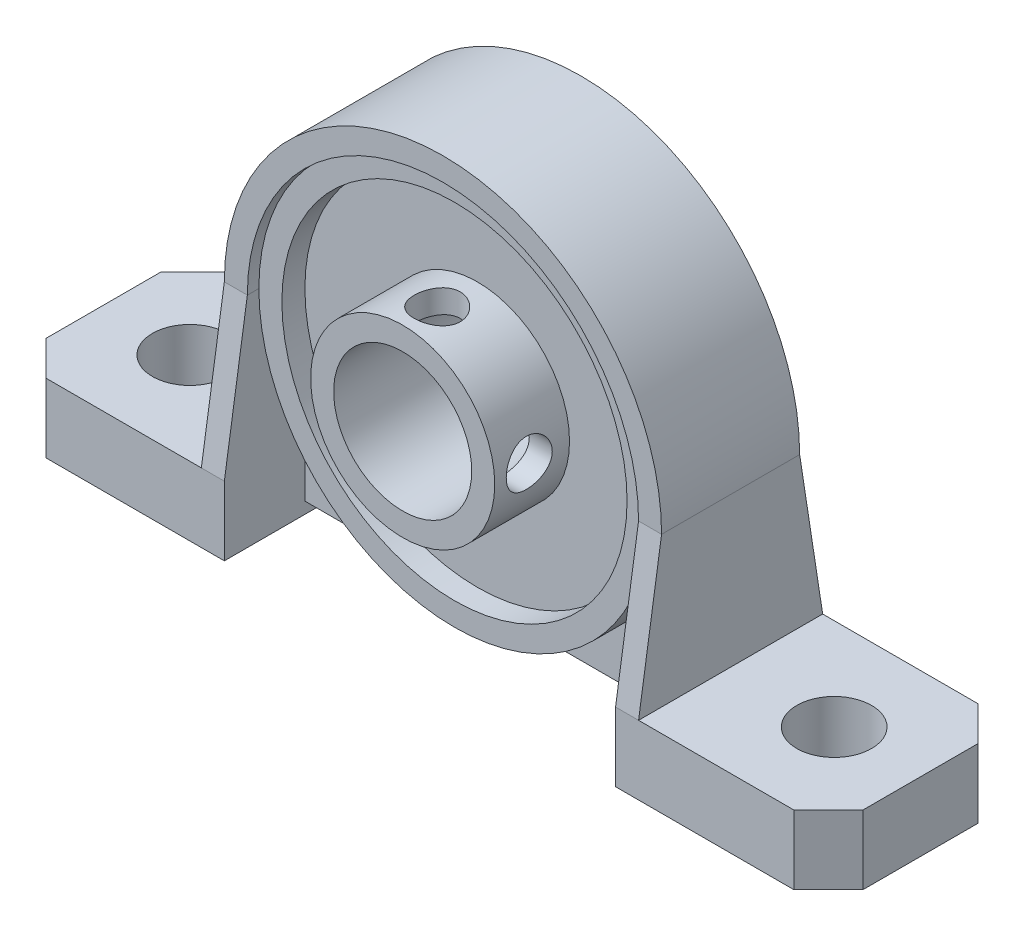
SolidWorks part; units mm, degrees
ref_plane "Front Plane" through (0, 0, 0) normal (0, 0, 1) x (1, 0, 0)
ref_plane "Top Plane" through (0, 0, 0) normal (0, 1, 0) x (1, 0, 0)
ref_plane "Right Plane" through (0, 0, 0) normal (1, 0, 0) x (0, 0, -1)
sketch "Sketch1" plane through (0, 0, 0) normal (0, 0, 1) x (1, 0, 0)
  line L0 (0, -3) -> (0, 16) construction
  line L1 (-35.5, 3) -> (-19, 3)
  line L2 (-35.5, 3) -> (-35.5, -3)
  line L3 (-35.5, -3) -> (-17, -3)
  line L4 (35.5, 3) -> (35.5, -3)
  line L5 (-35.5, 3) -> (35.5, -3) construction
  line L6 (-35.5, -3) -> (35.5, 3) construction
  line L7 (-19, 16) -> (-19, 3)
  line L8 (19, 16) -> (19, 3)
  line L11 (19, 3) -> (35.5, 3)
  line L12 (-17, 16) -> (-17, -3)
  line L13 (17, 16) -> (17, -3)
  line L14 (17, -3) -> (35.5, -3)
  arc A0 (19, 16) -> (-19, 16) centre (0, 16) ccw
  arc A2 (17, 16) -> (-17, 16) centre (0, 16) ccw
  point P0 (0, 0)
  dimension "D4" = 38
  dimension "D5" = 34
  dimension "D1" = 6
  dimension "D2" = 71
  dimension "D3" = 19
extrude "Boss-Extrude1" add sketch "Sketch1" along normal mid plane 16
chamfer "Chamfer1" distance 3 angle 45 4 edges at (35.5, 0, -8) (35.5, 0, 8) (-35.5, 0, -8) (-35.5, 0, 8)
sketch "Sketch3" plane through (0, 3, 0) normal (0, 1, 0) x (1, 0, 0)
  line L0 (0, 0) -> (28, 0) construction
  line L1 (0, -55) -> (0, 55) construction
  circle A0 centre (28, 0) radius 3.25
  circle A1 centre (-28, 0) radius 3.25
  dimension "D2" = 6.5
  dimension "D1" = 28
extrude "Cut-Extrude2" cut sketch "Sketch3" against normal blind 19
sketch "Sketch4" plane through (0, 0, 0) normal (0, 0, 1) x (1, 0, 0)
  line L0 (-17, 16) -> (0, 16) construction
  circle A0 centre (0, 16) radius 17
extrude "Boss-Extrude2" add sketch "Sketch4" along normal mid plane 6
sketch "Sketch5" plane through (0, 0, 3) normal (0, 0, 1) x (1, 0, 0)
  circle A0 centre (0, 16) radius 17
  circle A1 centre (0, 16) radius 15
  dimension "D1" = 34
  dimension "D2" = 30
extrude "Boss-Extrude3" add sketch "Sketch5" along normal blind 2
mirror "Mirror1" about plane through (0, 0, 0) normal (0, 0, 1) of "Boss-Extrude3"
sketch "Sketch6" plane through (0, 0, 3) normal (0, 0, 1) x (1, 0, 0)
  circle A0 centre (0, 16) radius 8
  dimension "D1" = 16
extrude "Boss-Extrude4" add sketch "Sketch6" along normal blind 6.5
sketch "Sketch7" plane through (0, 0, -3) normal (0, 0, -1) x (-1, 0, 0)
  circle A0 centre (0, 16) radius 8
  dimension "D1" = 16
extrude "Boss-Extrude5" add sketch "Sketch7" along normal blind 3
sketch "Sketch8" plane through (0, 0, 9.5) normal (0, 0, 1) x (1, 0, 0)
  circle A0 centre (0, 16) radius 6
  dimension "D1" = 12
extrude "Cut-Extrude3" cut sketch "Sketch8" against normal blind 23
ref_plane "Plane1" through (0, -2, 0) normal (0, 1, 0) x (1, 0, 0)
sketch "Sketch9" plane through (0, -2, 0) normal (0, 1, 0) x (1, 0, 0)
  line L1 (-17, -1) -> (17, -1)
  line L2 (-17, -1) -> (-17, 1)
  line L3 (-17, 1) -> (17, 1)
  line L4 (17, -1) -> (17, 1)
  line L5 (-17, -1) -> (17, 1) construction
  line L6 (-17, 1) -> (17, -1) construction
  line L7 (17, -8) -> (17, 8) construction
  point P0 (0, 0)
  dimension "D1" = 2
  dimension "D2" = 34
extrude "Boss-Extrude6" add sketch "Sketch9" along normal up to surface (18 mm away)
sketch "Sketch10" plane through (19, 0, 0) normal (1, 0, 0) x (0, 0, -1)
  line L0 (-8, 3) -> (-8, 16)
  line L1 (-8, 16) -> (-6, 16)
  line L2 (-8, 16) -> (8, 16) construction
  line L3 (-6, 16) -> (-8, 3)
  line L4 (0, 20.9) -> (0, -20.9) construction
  line L5 (6, 16) -> (8, 3)
  line L6 (8, 16) -> (6, 16)
  line L7 (8, 3) -> (8, 16)
  dimension "D1" = 2
extrude "Cut-Extrude4" cut sketch "Sketch10" against normal blind 2
mirror "Mirror2" about plane through (0, 0, 0) normal (1, 0, 0) of "Cut-Extrude4"
sketch "Sketch11" plane through (0, 16, 0) normal (0, -1, 0) x (1, 0, 0)
  line L5 (-17, 8) -> (-19, 8)
  line L6 (-17, 8) -> (-17, 6)
  line L7 (-17, 6) -> (-19, 6)
  line L8 (-19, 8) -> (-19, 6)
  line L9 (-17, -8) -> (-19, -8)
  line L10 (-17, -8) -> (-17, -6)
  line L11 (-17, -6) -> (-19, -6)
  line L12 (-19, -8) -> (-19, -6)
  dimension "D1" = 2
  dimension "D2" = 2
revolve "Cut-Revolve1" cut sketch "Sketch11" angle 180 about axis through (0, 16, 3) along (0, 0, -1)
sketch "Sketch12" plane through (0, 0, 0) normal (1, 0, 0) x (0, 0, -1)
  line L0 (-9.5, 16) -> (-6.5, 16) construction
  line L1 (-9.5, 24) -> (-9.5, 8) construction
  circle A0 centre (-6.5, 16) radius 2
  dimension "D2" = 4
  dimension "D1" = 3
extrude "Cut-Extrude5" cut sketch "Sketch12" along normal blind 12
ref_plane "Plane2" through (0, 20, 0) normal (0, 1, 0) x (1, 0, 0)
sketch "Sketch13" plane through (0, 20, 0) normal (0, 1, 0) x (1, 0, 0)
  line L0 (0, -9.5) -> (0, -6.5) construction
  line L1 (-8, -9.5) -> (8, -9.5) construction
  circle A0 centre (0, -6.5) radius 2
  dimension "D2" = 4
  dimension "D1" = 3
extrude "Cut-Extrude6" cut sketch "Sketch13" along normal blind 4
